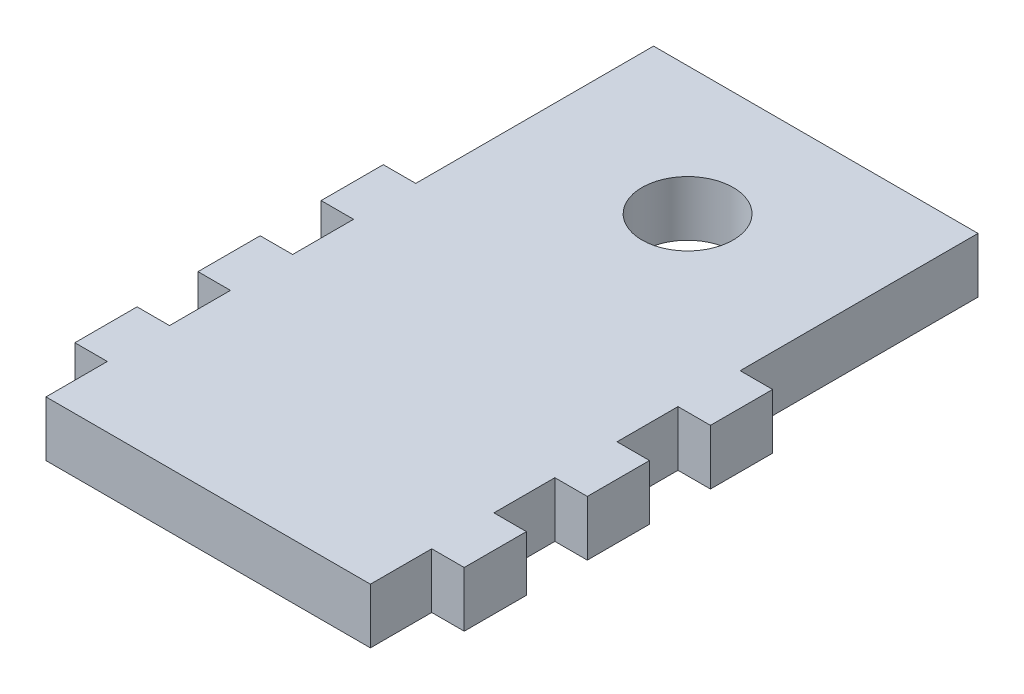
SolidWorks part; units mm, degrees
ref_plane "Front Plane" through (0, 0, 0) normal (0, 0, 1) x (1, 0, 0)
ref_plane "Top Plane" through (0, 0, 0) normal (0, 1, 0) x (1, 0, 0)
ref_plane "Right Plane" through (0, 0, 0) normal (1, 0, 0) x (0, 0, -1)
sketch "Sketch1" plane through (0, 0, 0) normal (0, 1, 0) x (1, 0, 0)
  line L0 (-3.4986, 29.7483) -> (-3.4986, -29.6017) construction
  line L1 (-19.3236, 29.7483) -> (12.3264, 29.7483)
  line L2 (-19.3236, 29.7483) -> (-19.3236, -29.6017)
  line L3 (-19.3236, -29.6017) -> (12.3264, -29.6017)
  line L4 (12.3264, 29.7483) -> (12.3264, -29.6017)
  line L5 (-19.3236, 17.2483) -> (12.3264, 17.2483) construction
  line L6 (-19.3236, -5.5588) -> (-22.4986, -5.5588)
  line L7 (-19.3236, -17.6017) -> (-22.4986, -17.6017)
  line L8 (-19.3236, -17.6017) -> (-19.3236, -23.6017)
  line L9 (-19.3236, -23.6017) -> (-22.4986, -23.6017)
  line L10 (-22.4986, -17.6017) -> (-22.4986, -23.6017)
  line L11 (-22.4986, -5.5588) -> (-22.4986, -11.5588)
  line L12 (-19.3236, -11.5588) -> (-22.4986, -11.5588)
  line L13 (-19.3236, 6.484) -> (-22.4986, 6.484)
  line L14 (-22.4986, 6.484) -> (-22.4986, 0.484)
  line L15 (-19.3236, 0.484) -> (-22.4986, 0.484)
  line L16 (12.3264, 0.484) -> (15.5014, 0.484)
  line L17 (15.5014, 6.484) -> (15.5014, 0.484)
  line L18 (12.3264, 6.484) -> (15.5014, 6.484)
  line L19 (12.3264, -11.5588) -> (15.5014, -11.5588)
  line L20 (15.5014, -5.5588) -> (15.5014, -11.5588)
  line L21 (15.5014, -17.6017) -> (15.5014, -23.6017)
  line L22 (12.3264, -23.6017) -> (15.5014, -23.6017)
  line L23 (12.3264, -17.6017) -> (12.3264, -23.6017)
  line L24 (12.3264, -17.6017) -> (15.5014, -17.6017)
  line L25 (12.3264, -5.5588) -> (15.5014, -5.5588)
  circle A0 centre (-3.4986, 17.2483) radius 4.5
  circle A1 centre (-3.4986, 17.2483) radius 2.5
  dimension "D1" = 9
  dimension "D2" = 5
  dimension "D3" = 46.85
  dimension "D4" = 31.65
  dimension "D5" = 59.35
  dimension "D6" = 6
  dimension "D7" = 6
  dimension "D8" = 3.175
  dimension "D10" = 6.0429
  dimension "D9" = 3
extrude "Boss-Extrude1" add sketch "Sketch1" along normal blind 5.4 contours L4 L1 L2 L3 A0 | L15 L2 L13 L14 | L12 L2 L6 L11 | L7 L10 L9 L2 | L24 L4 L22 L21 | L25 L4 L19 L20 | L18 L4 L16 L17
sketch "Sketch2" plane through (0, 5.4, 0) normal (0, 1, 0) x (1, 0, 0)
  line L168 (12.367, 6.5246) -> (12.367, 29.7889)
  line L169 (12.367, 29.7889) -> (-19.3643, 29.7889)
  line L170 (-19.3643, 29.7889) -> (-19.3643, 6.5246)
  line L171 (-19.3643, 6.5246) -> (-22.5393, 6.5246)
  line L172 (-22.5393, 6.5246) -> (-22.5393, 0.4434)
  line L173 (-22.5393, 0.4434) -> (-19.3643, 0.4434)
  line L174 (-19.3643, 0.4434) -> (-19.3643, -5.5182)
  line L175 (-19.3643, -5.5182) -> (-22.5393, -5.5182)
  line L176 (-22.5393, -5.5182) -> (-22.5393, -11.5995)
  line L177 (-22.5393, -11.5995) -> (-19.3643, -11.5995)
  line L178 (-19.3643, -11.5995) -> (-19.3643, -17.5611)
  line L179 (-19.3643, -17.5611) -> (-22.5393, -17.5611)
  line L180 (-22.5393, -17.5611) -> (-22.5393, -23.6423)
  line L181 (-22.5393, -23.6423) -> (-19.3643, -23.6423)
  line L182 (-19.3643, -23.6423) -> (-19.3643, -29.6423)
  line L183 (-19.3643, -29.6423) -> (12.367, -29.6423)
  line L184 (12.367, -29.6423) -> (12.367, -23.6423)
  line L185 (12.367, -23.6423) -> (15.542, -23.6423)
  line L186 (15.542, -23.6423) -> (15.542, -17.5611)
  line L187 (15.542, -17.5611) -> (12.367, -17.5611)
  line L188 (12.367, -17.5611) -> (12.367, -11.5995)
  line L189 (12.367, -11.5995) -> (15.542, -11.5995)
  line L190 (15.542, -11.5995) -> (15.542, -5.5182)
  line L191 (15.542, -5.5182) -> (12.367, -5.5182)
  line L192 (12.367, -5.5182) -> (12.367, 0.4434)
  line L193 (12.367, 0.4434) -> (15.542, 0.4434)
  line L194 (15.542, 0.4434) -> (15.542, 6.5246)
  line L195 (15.542, 6.5246) -> (12.367, 6.5246)
  line L196 (12.367, 6.5246) -> (12.367, 29.7889)
  line L197 (12.367, 29.7889) -> (-19.3643, 29.7889)
  line L198 (-19.3643, 29.7889) -> (-19.3643, 6.5246)
  line L199 (-19.3643, 6.5246) -> (-22.5393, 6.5246)
  line L200 (-22.5393, 6.5246) -> (-22.5393, 0.4434)
  line L201 (-22.5393, 0.4434) -> (-19.3643, 0.4434)
  line L202 (-19.3643, 0.4434) -> (-19.3643, -5.5182)
  line L203 (-19.3643, -5.5182) -> (-22.5393, -5.5182)
  line L204 (-22.5393, -5.5182) -> (-22.5393, -11.5995)
  line L205 (-22.5393, -11.5995) -> (-19.3643, -11.5995)
  line L206 (-19.3643, -11.5995) -> (-19.3643, -17.5611)
  line L207 (-19.3643, -17.5611) -> (-22.5393, -17.5611)
  line L208 (-22.5393, -17.5611) -> (-22.5393, -23.6423)
  line L209 (-22.5393, -23.6423) -> (-19.3643, -23.6423)
  line L210 (-19.3643, -23.6423) -> (-19.3643, -29.6423)
  line L211 (-19.3643, -29.6423) -> (12.367, -29.6423)
  line L212 (12.367, -29.6423) -> (12.367, -23.6423)
  line L213 (12.367, -23.6423) -> (15.542, -23.6423)
  line L214 (15.542, -23.6423) -> (15.542, -17.5611)
  line L215 (15.542, -17.5611) -> (12.367, -17.5611)
  line L216 (12.367, -17.5611) -> (12.367, -11.5995)
  line L217 (12.367, -11.5995) -> (15.542, -11.5995)
  line L218 (15.542, -11.5995) -> (15.542, -5.5182)
  line L219 (15.542, -5.5182) -> (12.367, -5.5182)
  line L220 (12.367, -5.5182) -> (12.367, 0.4434)
  line L221 (12.367, 0.4434) -> (15.542, 0.4434)
  line L222 (15.542, 0.4434) -> (15.542, 6.5246)
  line L223 (15.542, 6.5246) -> (12.367, 6.5246)
  circle A2 centre (-3.4986, 17.2483) radius 4.4594
  circle A4 centre (-3.4986, 17.2483) radius 4.4594
  dimension "D1" = 0.0406
  dimension "D2" = 0.0406
extrude "Boss-Extrude2" add sketch "Sketch2" against normal up to surface (5.4 mm away) up to face at (-3.4986, 0, -12.7483)
equation "\"stepper holder width\"= 4.23"
equation "\"tooth width\"= \"stepper holder width\" / 7"
equation "\"D10@Sketch1\"=\"tooth width\""
